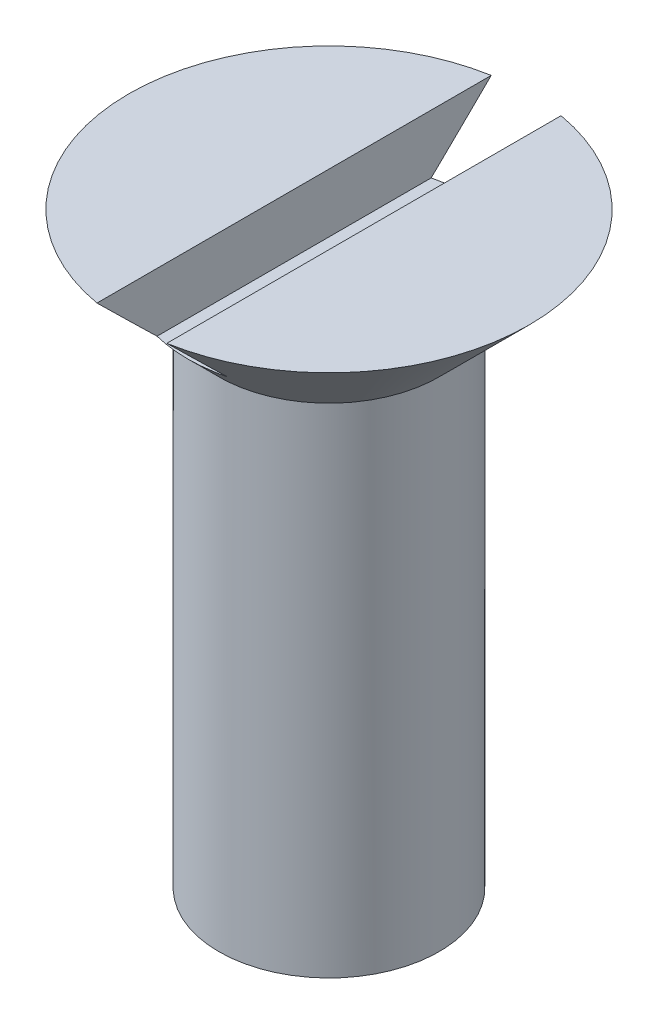
SolidWorks part; units mm, degrees
ref_plane "Front Plane" through (0, 0, 0) normal (0, 0, 1) x (1, 0, 0)
ref_plane "Top Plane" through (0, 0, 0) normal (0, 1, 0) x (1, 0, 0)
ref_plane "Right Plane" through (0, 0, 0) normal (1, 0, 0) x (0, 0, -1)
sketch "Sketch1" plane through (0, 0, 0) normal (0, 0, 1) x (1, 0, 0)
  line L0 (0, 0) -> (0, 17.7321) construction
  line L2 (5.45, 17.7321) -> (3, 15.2821)
  line L3 (3, 15.2821) -> (3, 1.7321)
  line L4 (3, 1.7321) -> (0, 0)
  line L5 (0, 0) -> (18.0915, 0) construction
  line L6 (-3, 1.7321) -> (0, 0) construction
  line L7 (-3, 15.2821) -> (-3, 1.7321) construction
  line L8 (-5.45, 17.7321) -> (-3, 15.2821) construction
  line L9 (5.45, 17.7321) -> (0, 17.7321)
  line L10 (0, 17.7321) -> (-5.45, 17.7321) construction
  line L11 (0, 0) -> (0, 17.7321)
  line L12 (0, 17.7321) -> (0, 0)
  dimension "D1" = 120
  dimension "D2" = 90
  dimension "D3" = 10.9
  dimension "D4" = 6
  dimension "D5" = 16
revolve "Revolve1" add sketch "Sketch1" angle 360 about L0
sketch "Sketch2" plane through (0, 0, 0) normal (0, 0, 1) x (1, 0, 0)
  line L0 (0, 17.7321) -> (0, 17.1396) construction
  line L2 (5.45, 17.7321) -> (-5.45, 17.7321) construction
  line L3 (-0.95, 17.7321) -> (0.95, 17.7321)
  line L4 (-0.95, 17.7321) -> (-0.95, 16.1321)
  line L5 (-0.95, 16.1321) -> (0.95, 16.1321)
  line L6 (0.95, 17.7321) -> (0.95, 16.1321)
  dimension "D1" = 1.9
  dimension "D2" = 1.6
extrude "Cut-Extrude1" cut sketch "Sketch2" against normal through all both and the other way through all
